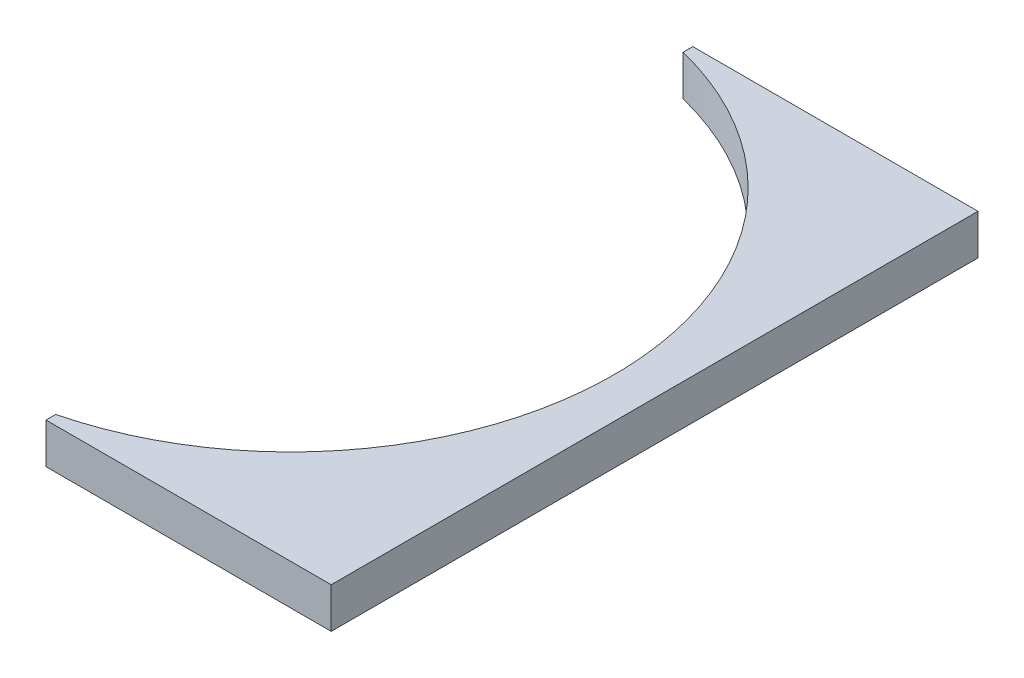
SolidWorks part; units mm, degrees
ref_plane "Front Plane" through (0, 0, 0) normal (0, 0, 1) x (1, 0, 0)
ref_plane "Top Plane" through (0, 0, 0) normal (0, 1, 0) x (1, 0, 0)
ref_plane "Right Plane" through (0, 0, 0) normal (1, 0, 0) x (0, 0, -1)
sketch "Sketch1" plane through (0, 0, 0) normal (0, 1, 0) x (1, 0, 0)
  line L4 (6.1749, 25.4) -> (28.575, 25.4)
  line L5 (28.575, 25.4) -> (28.575, -25.4)
  line L6 (28.575, -25.4) -> (6.1749, -25.4)
  line L7 (6.1749, -25.4) -> (6.1749, -24.638)
  line L8 (6.1749, 25.4) -> (6.1749, 24.638)
  line L9 (0, 0) -> (0, 25.4) construction
  circle A2 centre (0, 0) radius 25.4
  dimension "D1" = 50.8
  dimension "D2" = 0.762
  dimension "D3" = 0.762
  dimension "D4" = 28.575
extrude "Boss-Extrude1" add sketch "Sketch1" along normal blind 3.175 contours A2 L7 L6 L5 L4 L8
